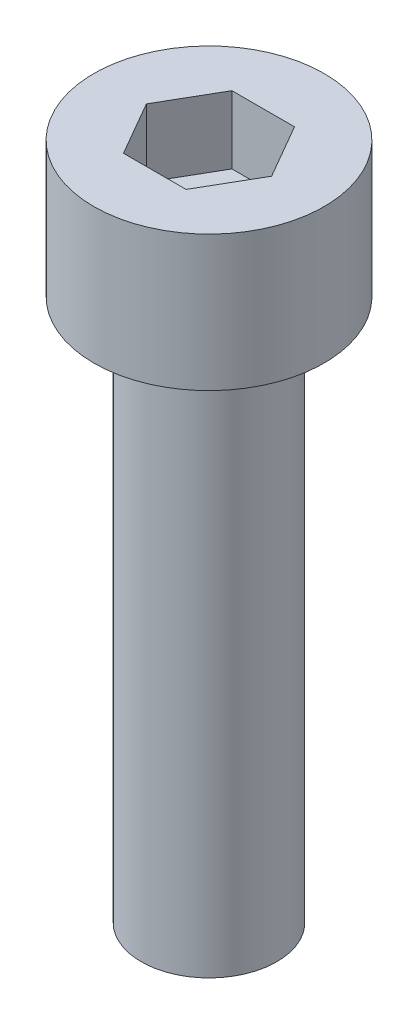
SolidWorks part; units mm, degrees
material "AISI 304"
ref_plane "前视基准面" through (0, 0, 0) normal (0, 0, 1) x (1, 0, 0)
ref_plane "上视基准面" through (0, 0, 0) normal (0, 1, 0) x (1, 0, 0)
ref_plane "右视基准面" through (0, 0, 0) normal (1, 0, 0) x (0, 0, -1)
sketch "草图1" plane through (0, 0, 0) normal (0, 1, 0) x (1, 0, 0)
  circle A0 centre (0, 0) radius 4.25
  dimension "D1" = 8.5
extrude "凸台-拉伸1" add sketch "草图1" along normal blind 5
sketch "草图2" plane through (0, 5, 0) normal (0, 1, 0) x (1, 0, 0)
  line L1 (2.3094, 0) -> (1.1547, 2)
  line L2 (1.1547, 2) -> (-1.1547, 2)
  line L3 (-1.1547, 2) -> (-2.3094, 0)
  line L4 (-2.3094, 0) -> (-1.1547, -2)
  line L5 (-1.1547, -2) -> (1.1547, -2)
  line L6 (1.1547, -2) -> (2.3094, 0)
  circle A0 centre (0, 0) radius 2 construction
  dimension "D1" = 4
extrude "切除-拉伸1" cut sketch "草图2" against normal blind 2.5
sketch "草图3" plane through (0, 0, 0) normal (0, -1, 0) x (1, 0, 0)
  circle A0 centre (0, 0) radius 2.5
  dimension "D1" = 5
extrude "凸台-拉伸2" add sketch "草图3" along normal blind 20
